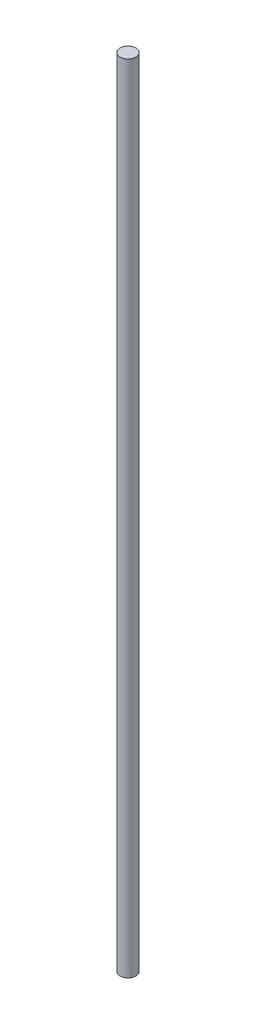
SolidWorks part; units mm, degrees
ref_plane "Front" through (0, 0, 0) normal (0, 0, 1) x (1, 0, 0)
ref_plane "Top" through (0, 0, 0) normal (0, 1, 0) x (1, 0, 0)
ref_plane "Right" through (0, 0, 0) normal (1, 0, 0) x (0, 0, -1)
sketch "Skica1" plane through (0, 0, 0) normal (0, 1, 0) x (1, 0, 0)
  circle A0 centre (0, 0) radius 4
  dimension "D1" = 8
extrude "Přidat vysunutím1" add sketch "Skica1" along normal blind 400
